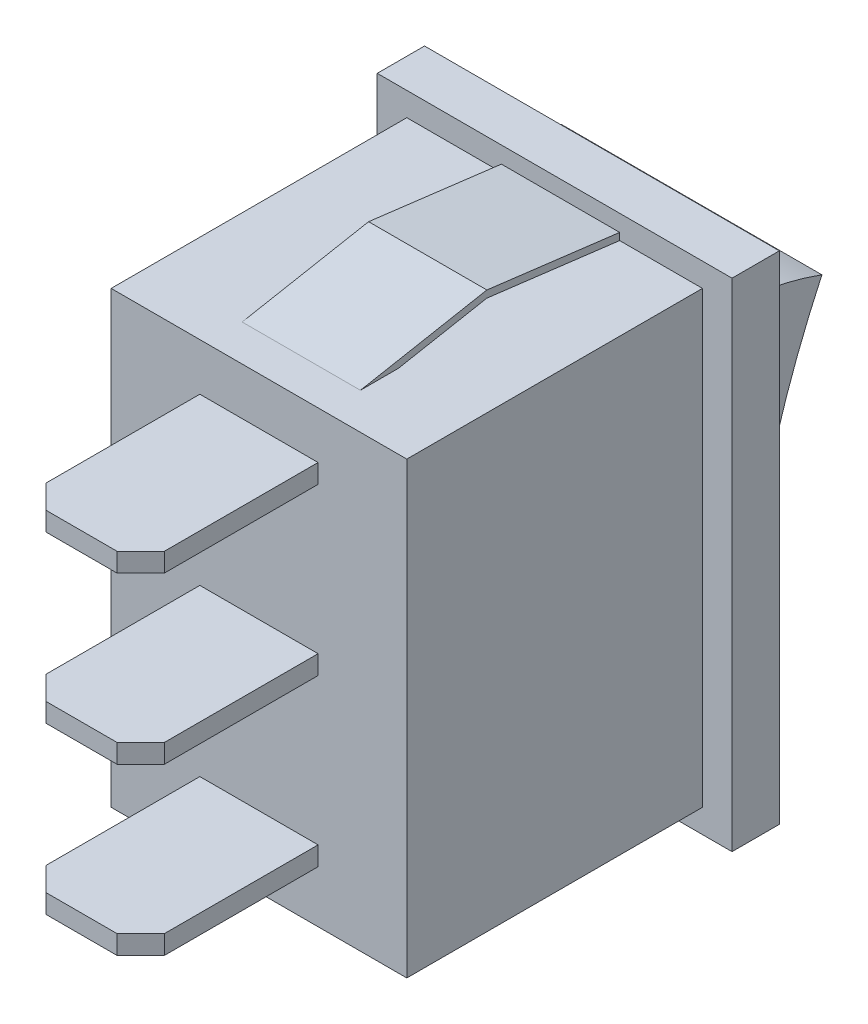
SolidWorks part; units mm, degrees
ref_plane "Спереди" through (0, 0, 0) normal (0, 0, 1) x (1, 0, 0)
ref_plane "Сверху" through (0, 0, 0) normal (0, 1, 0) x (1, 0, 0)
ref_plane "Справа" through (0, 0, 0) normal (1, 0, 0) x (0, 0, -1)
sketch "Эскиз1" plane through (0, 0, 0) normal (0, 0, 1) x (1, 0, 0)
  line L1 (-142.9721, 52.8695) -> (-127.9721, 52.8695)
  line L2 (-142.9721, 52.8695) -> (-142.9721, 31.8695)
  line L3 (-142.9721, 31.8695) -> (-127.9721, 31.8695)
  line L4 (-127.9721, 52.8695) -> (-127.9721, 31.8695)
  line L5 (-142.9721, 52.8695) -> (-127.9721, 31.8695) construction
  line L6 (-142.9721, 31.8695) -> (-127.9721, 52.8695) construction
  point P0 (-135.4721, 42.3695)
extrude "Бобышка-Вытянуть1" add sketch "Эскиз1" along normal blind 2
sketch "Эскиз2" plane through (0, 0, 2) normal (0, 0, 1) x (1, 0, 0)
  line L0 (-142.9721, 52.8695) -> (-127.9721, 31.8695) construction
  line L2 (-141.7221, 51.8695) -> (-129.2221, 51.8695)
  line L3 (-141.7221, 51.8695) -> (-141.7221, 32.8695)
  line L4 (-141.7221, 32.8695) -> (-129.2221, 32.8695)
  line L5 (-129.2221, 51.8695) -> (-129.2221, 32.8695)
  line L6 (-141.7221, 51.8695) -> (-129.2221, 32.8695) construction
  line L7 (-141.7221, 32.8695) -> (-129.2221, 51.8695) construction
  point P4 (-135.4721, 42.3695)
extrude "Бобышка-Вытянуть2" add sketch "Эскиз2" along normal blind 12.5
sketch "Эскиз3" plane through (0, 0, 14.5) normal (0, 0, 1) x (1, 0, 0)
  line L0 (-129.2221, 51.8695) -> (-141.7221, 51.8695) construction
  line L1 (-137.9721, 49.8695) -> (-132.9721, 49.8695)
  line L2 (-137.9721, 49.8695) -> (-137.9721, 49.0695)
  line L3 (-137.9721, 49.0695) -> (-132.9721, 49.0695)
  line L4 (-132.9721, 49.8695) -> (-132.9721, 49.0695)
  line L5 (-137.9721, 49.8695) -> (-132.9721, 49.0695) construction
  line L6 (-137.9721, 49.0695) -> (-132.9721, 49.8695) construction
  line L7 (-142.9721, 52.8695) -> (-142.9721, 31.8695) construction
  line L8 (-137.9721, 42.8695) -> (-132.9721, 42.8695)
  line L9 (-137.9721, 42.8695) -> (-137.9721, 42.0695)
  line L10 (-137.9721, 42.0695) -> (-132.9721, 42.0695)
  line L11 (-132.9721, 42.8695) -> (-132.9721, 42.0695)
  line L12 (-137.9721, 35.8695) -> (-132.9721, 35.8695)
  line L13 (-137.9721, 35.8695) -> (-137.9721, 35.0695)
  line L14 (-137.9721, 35.0695) -> (-132.9721, 35.0695)
  line L15 (-132.9721, 35.8695) -> (-132.9721, 35.0695)
  point P0 (-135.4721, 49.4695)
  dimension "D1" = 2
  dimension "D2" = 5
  dimension "D3" = 5
  dimension "D4" = 0.8
  dimension "D5" = 3
extrude "Бобышка-Вытянуть3" add sketch "Эскиз3" along normal blind 7.5
chamfer "Фаска1" distance 1 angle 45 6 edges at (-132.9721, 49.4695, 22) (-132.9721, 42.4695, 22) (-132.9721, 35.4695, 22) (-137.9721, 49.4695, 22) (-137.9721, 42.4695, 22) (-137.9721, 35.4695, 22)
sketch "Эскиз5" plane through (-127.9721, 0, 0) normal (1, 0, 0) x (0, 0, -1)
  line L0 (0, 31.8695) -> (0, 52.8695) construction
  line L2 (0, 49.8695) -> (0, 34.8695)
  line L3 (0, 34.8695) -> (0.3542, 34.8695)
  line L6 (-2, 31.8695) -> (0, 31.8695) construction
  arc A0 (0, 49.8695) -> (3.8, 49.0921) centre (-0.6141, 37.1925) cw
  arc A1 (3.8, 49.0921) -> (0.3542, 34.8695) centre (37.0239, 33.514) ccw
  dimension "D2" = 3
extrude "Бобышка-Вытянуть4" add sketch "Эскиз5" against normal blind 11 from offset 2 offset against normal yes
sketch "Эскиз6" plane through (-129.2221, 0, 0) normal (1, 0, 0) x (0, 0, -1)
  line L0 (-2, 51.8695) -> (-2, 52.1695)
  line L1 (-2, 31.8695) -> (-2, 52.8695) construction
  line L2 (-2, 52.1695) -> (-7.6153, 52.8695)
  line L3 (-7.6153, 52.8695) -> (-12.9605, 51.8695)
  line L4 (-14.5, 51.8695) -> (-2, 51.8695) construction
  line L5 (-2, 51.8695) -> (-7.6153, 52.5695)
  line L7 (-7.6153, 52.5695) -> (-11.3569, 51.8695)
  line L8 (-12.9605, 51.8695) -> (-11.3569, 51.8695)
  line L9 (-2, 42.3695) -> (-4.8385, 42.3695) construction
  line L10 (-12.9605, 32.8695) -> (-11.3569, 32.8695)
  line L11 (-7.6153, 32.1695) -> (-11.3569, 32.8695)
  line L12 (-2, 32.8695) -> (-7.6153, 32.1695)
  line L13 (-7.6153, 31.8695) -> (-12.9605, 32.8695)
  line L14 (-2, 32.5695) -> (-7.6153, 31.8695)
  line L15 (-2, 32.8695) -> (-2, 32.5695)
extrude "Бобышка-Вытянуть5" add sketch "Эскиз6" against normal blind 5 from offset 3.5 offset against normal yes
